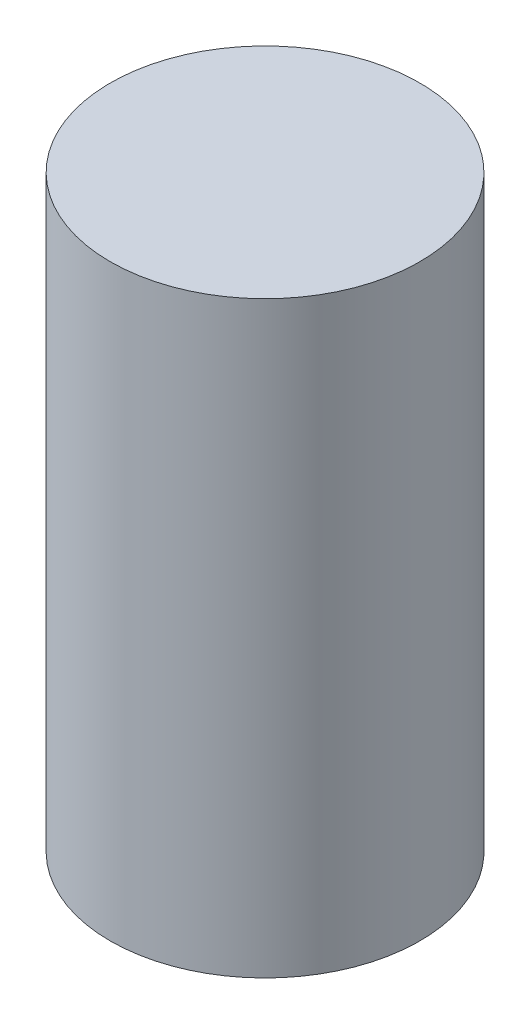
SolidWorks part; units mm, degrees
ref_plane "Front Plane" through (0, 0, 0) normal (0, 0, 1) x (1, 0, 0)
ref_plane "Top Plane" through (0, 0, 0) normal (0, 1, 0) x (1, 0, 0)
ref_plane "Right Plane" through (0, 0, 0) normal (1, 0, 0) x (0, 0, -1)
sketch "Sketch1" plane through (0, 0, 0) normal (0, 1, 0) x (1, 0, 0)
  circle A0 centre (0, 0) radius 6.35
  dimension "D1" = 12.7
extrude "Boss-Extrude1" add sketch "Sketch1" along normal blind 24.13 contours A0
